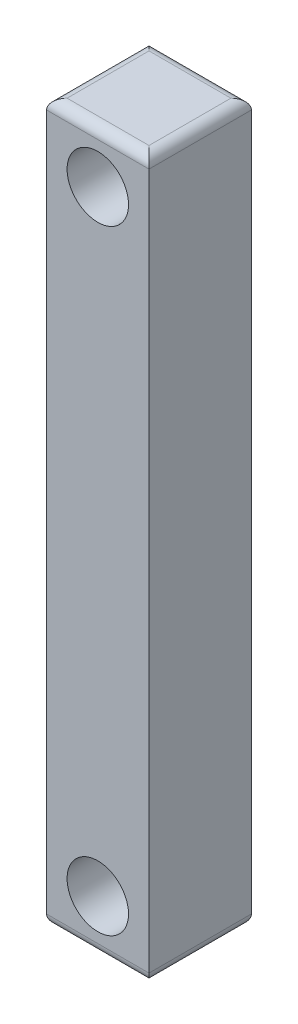
SolidWorks part; units mm, degrees
ref_plane "Front" through (0, 0, 0) normal (0, 0, 1) x (1, 0, 0)
ref_plane "Top" through (0, 0, 0) normal (0, 1, 0) x (1, 0, 0)
ref_plane "Right" through (0, 0, 0) normal (1, 0, 0) x (0, 0, -1)
sketch "Sketch1" plane through (0, 0, 0) normal (0, 0, 1) x (1, 0, 0)
  line L1 (-20.5497, 69.7557) -> (4.8503, 69.7557)
  line L2 (-20.5497, 69.7557) -> (-20.5497, -108.0443)
  line L3 (-20.5497, -108.0443) -> (4.8503, -108.0443)
  line L4 (4.8503, 69.7557) -> (4.8503, -108.0443)
  dimension "D1" = 25.4
  dimension "D2" = 177.8
extrude "Base-Extrude" add sketch "Sketch1" along normal blind 25.4
sketch "Sketch2" plane through (0, 0, 25.4) normal (0, 0, 1) x (1, 0, 0)
  line L0 (-7.8497, 69.7557) -> (-7.8497, -108.0443) construction
  line L1 (4.8503, 69.7557) -> (-20.5497, 69.7557) construction
  line L2 (-20.5497, -108.0443) -> (4.8503, -108.0443) construction
  circle A0 centre (-7.8497, -95.3443) radius 7.62
  circle A1 centre (-7.8497, 57.0557) radius 7.62
  dimension "D1" = 12.7
  dimension "D2" = 12.7
extrude "Cut-Extrude1" cut sketch "Sketch2" against normal blind 78.74
fillet "Fillet1" radius 2.54
